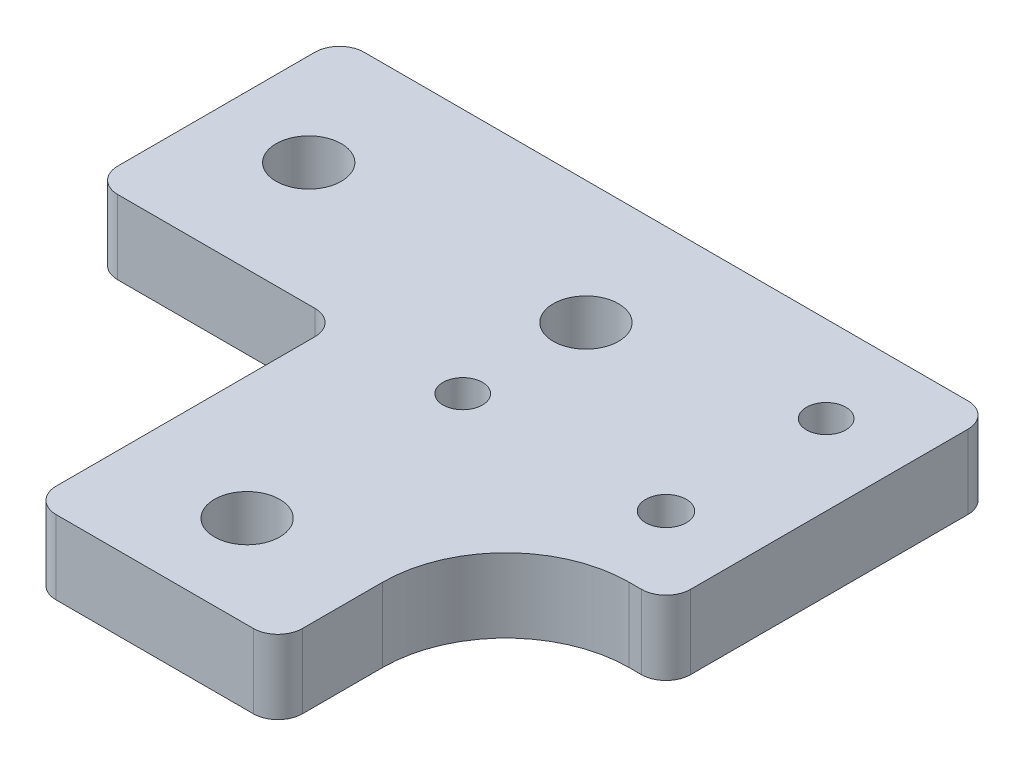
SolidWorks part; units mm, degrees
ref_plane "Front Plane" through (0, 0, 0) normal (0, 0, 1) x (1, 0, 0)
ref_plane "Top Plane" through (0, 0, 0) normal (0, 1, 0) x (1, 0, 0)
ref_plane "Right Plane" through (0, 0, 0) normal (1, 0, 0) x (0, 0, -1)
ref_plane "Plane1" through (0, 6, 0) normal (0, 1, 0) x (1, 0, 0)
sketch "Sketch1" plane through (0, 6, 0) normal (0, 1, 0) x (1, 0, 0)
  line L0 (104, 0) -> (55, 0)
  line L1 (53, -2) -> (53, -18)
  line L2 (55, -20) -> (71, -20)
  line L3 (73, -22) -> (73, -43)
  line L4 (75, -45) -> (91, -45)
  line L5 (93, -43) -> (93, -36.5)
  line L6 (103, -26.5) -> (104, -26.5)
  line L7 (106, -24.5) -> (106, -2)
  arc A0 (55, 0) -> (53, -2) centre (55, -2) ccw
  arc A1 (53, -18) -> (55, -20) centre (55, -18) ccw
  arc A2 (71, -20) -> (73, -22) centre (71, -22) cw
  arc A3 (73, -43) -> (75, -45) centre (75, -43) ccw
  arc A4 (91, -45) -> (93, -43) centre (91, -43) ccw
  arc A5 (93, -36.5) -> (103, -26.5) centre (103, -36.5) cw
  arc A6 (104, -26.5) -> (106, -24.5) centre (104, -24.5) ccw
  arc A7 (106, -2) -> (104, 0) centre (104, -2) ccw
  circle A8 centre (99.5, -20) radius 1.65
  circle A9 centre (99.5, -7) radius 1.6
  circle A10 centre (83, -20) radius 1.6
  circle A11 centre (83, -10) radius 2.65
  circle A12 centre (60.5, -10) radius 2.65
  circle A13 centre (83, -37.5) radius 2.65
  point P36 (103.5, -26.5)
  point P37 (0, 0)
  dimension "D9" = 2
  dimension "D12" = 2
  dimension "D13" = 2
  dimension "D14" = 2
  dimension "D15" = 2
  dimension "D16" = 5.3
  dimension "D17" = 5.3
  dimension "D18" = 5.3
  dimension "D19" = 2
  dimension "D22" = 3.2
  dimension "D23" = 3.2
  dimension "D24" = 3.3
  dimension "D25" = 10
  dimension "D27" = 2
  dimension "D1" = 20
  dimension "D2" = 20
  dimension "D3" = 25
  dimension "D4" = 53
  dimension "D5" = 10
  dimension "D6" = 7.5
  dimension "D7" = 22.5
  dimension "D8" = 27.5
  dimension "D10" = 6.5
  dimension "D11" = 26.5
  dimension "D20" = 16.5
  dimension "D21" = 13
  dimension "D26" = 20
  dimension "D28" = 10
  dimension "D29" = 7.5
  dimension "D30" = 7
extrude "Boss-Extrude1" add sketch "Sketch1" against normal blind 6
